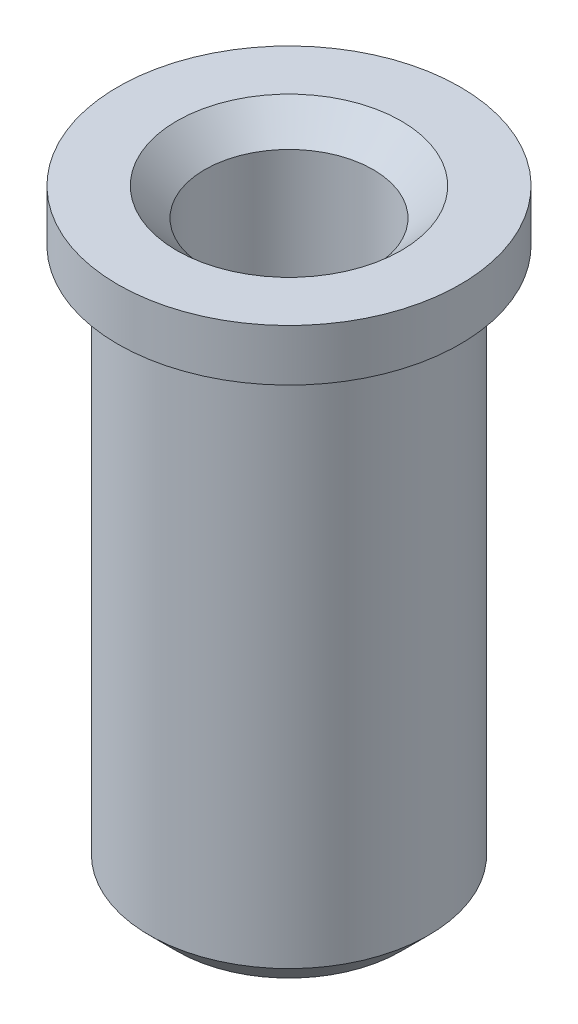
SolidWorks part; units mm, degrees
ref_plane "Front Plane" through (0, 0, 0) normal (0, 0, 1) x (1, 0, 0)
ref_plane "Top Plane" through (0, 0, 0) normal (0, 1, 0) x (1, 0, 0)
ref_plane "Right Plane" through (0, 0, 0) normal (1, 0, 0) x (0, 0, -1)
sketch "Sketch1" plane through (0, 0, 0) normal (1, 0, 0) x (0, 0, -1)
  line L0 (0, 0) -> (0, 2176.3106) construction
  line L1 (0, 2.705) -> (1.525, 2.705)
  line L2 (1.525, 2.705) -> (1.525, 2.245)
  line L3 (1.525, 2.245) -> (1.245, 2.245)
  line L4 (1.245, 2.245) -> (1.245, -2.705)
  line L5 (1.245, -2.705) -> (0, -2.705)
  line L6 (0, -2.705) -> (0, 2.705)
  point P8 (0, 0)
  dimension "D1" = 3.05
  dimension "D2" = 2.49
  dimension "D3" = 0.46
  dimension "D4" = 5.41
revolve "Revolve1" add sketch "Sketch1" angle 360 about L0
hole_wizard "Ø1.5 (1.5) Diameter Hole1" positions "3DSketch1" profile "Sketch2" hole size "Ø1.5" standard "ANSI Metric"
sketch3d "3DSketch1"
  line L0 (0, 2.705, 0) -> (0, 2.245, 0) construction
  point P0 (0, 2.705, 0)
sketch "Sketch2" plane through (0, 2.705, 0) normal (1, 0, 0) x (0, 0, 1)
  line L0 (0, 0) -> (0, 5.0206)
  line L1 (0, 5.0206) -> (0.75, 4.57)
  line L2 (0.75, 4.57) -> (0.75, 0)
  line L5 (0.75, 0) -> (0, 0)
  line L10 (0, 5.0206) -> (-0.75, 4.57) construction
  line L11 (0, -6.35) -> (0, 107.95) construction
  dimension "Hole Dia." = 1.5
  dimension "Hole Depth" = 4.57
  dimension "Drill Angle" = 118
chamfer "Chamfer1" distance 0.25 angle 45 1 edges at (0, -2.705, -1.245)
chamfer "Chamfer2" distance 0.25 angle 45 1 edges at (0, 2.705, 0.75)
